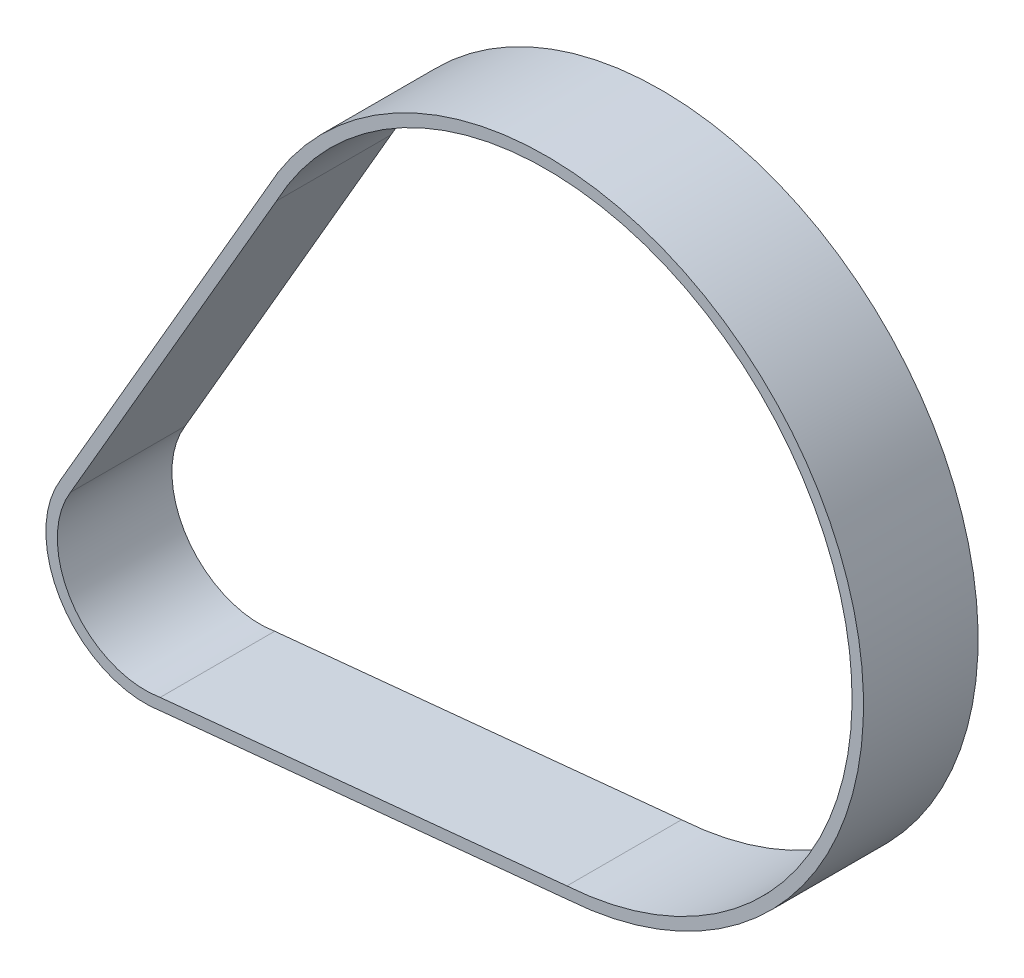
SolidWorks part; units mm, degrees
material "Rubber"
ref_plane "Front Plane" through (0, 0, 0) normal (0, 0, 1) x (1, 0, 0)
ref_plane "Top Plane" through (0, 0, 0) normal (0, 1, 0) x (1, 0, 0)
ref_plane "Right Plane" through (0, 0, 0) normal (1, 0, 0) x (0, 0, -1)
sketch "Sketch1" plane through (0, 0, 0) normal (0, 0, 1) x (1, 0, 0)
  line L0 (-9.7878, 6.0373) -> (17.1812, 52.5503)
  line L5 (55.2072, -6.0784) -> (1.9609, -11.3316)
  line L6 (-11.0755, 6.8068) -> (15.8692, 53.2779)
  line L7 (55.3313, -7.5734) -> (2.161, -12.8191)
  arc A4 (-9.7878, 6.0373) -> (1.9609, -11.3316) centre (0, 0) ccw
  arc A5 (55.2072, -6.0784) -> (17.1812, 52.5503) centre (52.5313, 33.832) ccw
  arc A6 (55.3313, -7.5734) -> (15.8692, 53.2779) centre (52.5313, 33.832) ccw
  arc A7 (-11.0755, 6.8068) -> (2.161, -12.8191) centre (0, 0) ccw
  point P6 (19.8708, 39.2288)
  point P14 (30.8514, -18.3324)
  point P15 (4.3588, 37.6272)
  point P16 (-11.4996, 5.3985)
  point P17 (-4.6754, -11.8989)
  point P18 (18.2042, 52.7888)
  point P19 (55.2302, -5.6407)
  point P20 (1.9609, -12.8191)
  dimension "D1" = 300
  dimension "D2" = 40
  dimension "D3" = 11.5
  dimension "D4" = 1.5
extrude "Boss-Extrude1" add sketch "Sketch1" along normal blind 15
